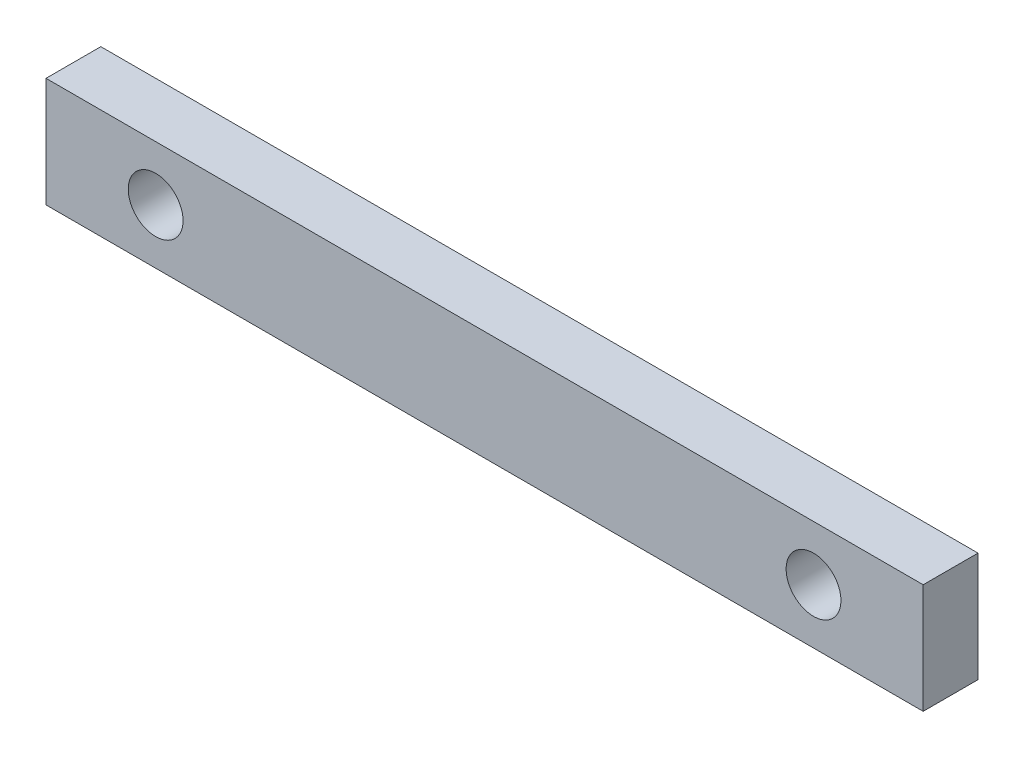
SolidWorks part; units mm, degrees
ref_plane "Front Plane" through (0, 0, 0) normal (0, 0, 1) x (1, 0, 0)
ref_plane "Top Plane" through (0, 0, 0) normal (0, 1, 0) x (1, 0, 0)
ref_plane "Right Plane" through (0, 0, 0) normal (1, 0, 0) x (0, 0, -1)
sketch "Sketch1" plane through (0, 0, 0) normal (0, 0, 1) x (1, 0, 0)
  line L0 (0, 0) -> (0, 5) construction
  line L1 (-40, 5) -> (40, 5)
  line L2 (-40, 5) -> (-40, -5)
  line L3 (-40, -5) -> (40, -5)
  line L4 (40, 5) -> (40, -5)
  line L5 (-40, 5) -> (40, -5) construction
  line L6 (-40, -5) -> (40, 5) construction
  circle A0 centre (-30, 0) radius 2.5
  circle A1 centre (30, 0) radius 2.5
  point P0 (0, 0)
  dimension "D4" = 5
  dimension "D1" = 80
  dimension "D2" = 10
  dimension "D3" = 10
extrude "Boss-Extrude1" add sketch "Sketch1" along normal blind 5
